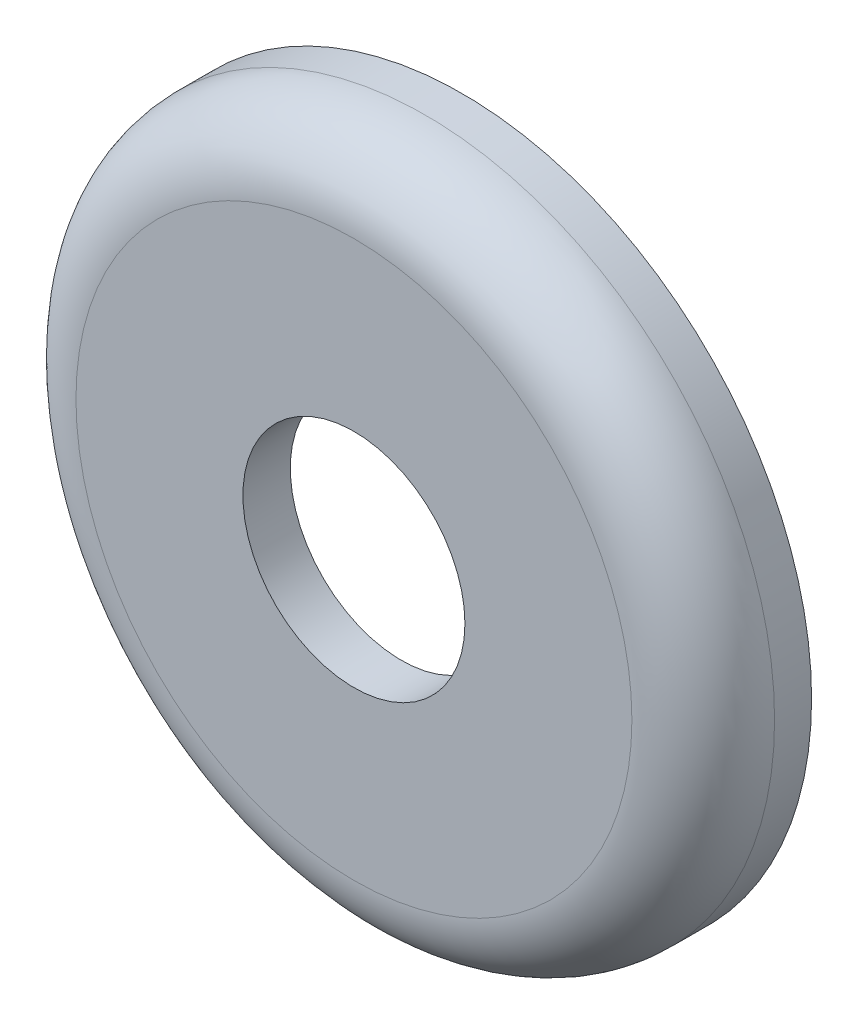
SolidWorks part; units mm, degrees
ref_plane "Front Plane" through (0, 0, 0) normal (0, 0, 1) x (1, 0, 0)
ref_plane "Top Plane" through (0, 0, 0) normal (0, 1, 0) x (1, 0, 0)
ref_plane "Right Plane" through (0, 0, 0) normal (1, 0, 0) x (0, 0, -1)
sketch "Sketch1" plane through (0, 0, 0) normal (0, 1, 0) x (1, 0, 0)
  line L0 (0, 0) -> (0, 5.3831)
  line L1 (4.7625, 2.032) -> (4.7625, 0)
  line L2 (4.7625, 0) -> (11.9253, 0)
  line L3 (14.986, 3.0607) -> (14.986, 4.6482)
  line L4 (14.986, 4.6482) -> (13.3985, 4.6482)
  line L5 (13.3985, 4.6482) -> (12.9498, 2.3527)
  line L6 (4.7625, 2.032) -> (12.5603, 2.032)
  arc A0 (11.9253, 0) -> (14.986, 3.0607) centre (11.9253, 3.0607) ccw
  arc A1 (12.5603, 2.032) -> (12.9498, 2.3527) centre (12.5603, 2.4289) ccw
  dimension "D1" = 4.7625
  dimension "D8" = 12.5603
  dimension "D6" = 0.3969
  dimension "D2" = 2.032
  dimension "D3" = 14.986
  dimension "D4" = 4.6482
  dimension "D5" = 1.5875
  dimension "D7" = 1.5875
revolve "Revolve1" add sketch "Sketch1" angle 360 about L0
